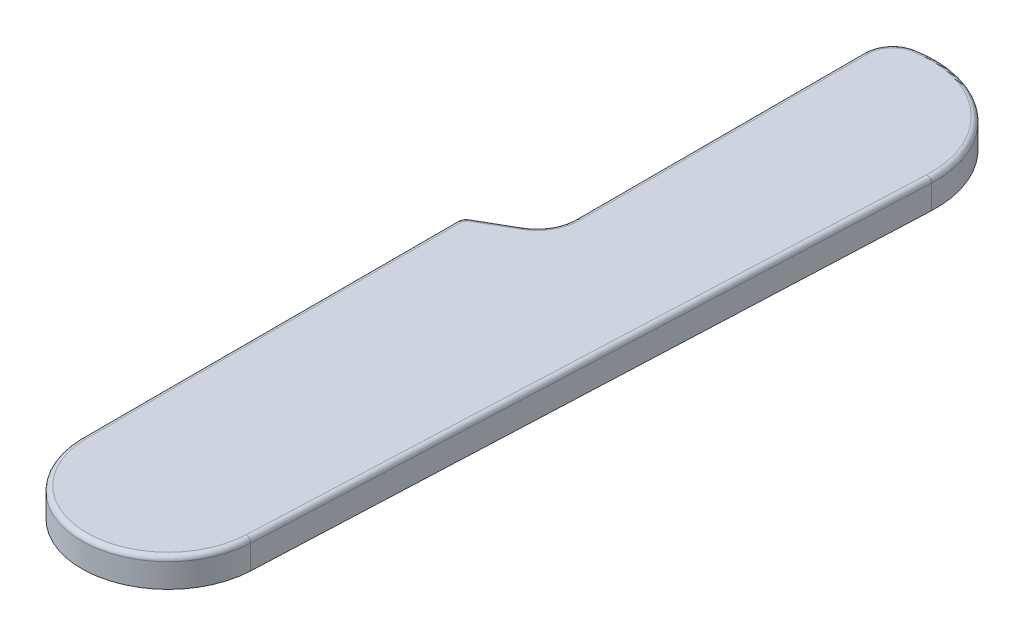
SolidWorks part; units mm, degrees
material "1060 Alloy"
ref_plane "Front Plane" through (0, 0, 0) normal (0, 0, 1) x (1, 0, 0)
ref_plane "Top Plane" through (0, 0, 0) normal (0, 1, 0) x (1, 0, 0)
ref_plane "Right Plane" through (0, 0, 0) normal (1, 0, 0) x (0, 0, -1)
sketch "Sketch1" plane through (0, 0, 0) normal (0, 1, 0) x (1, 0, 0)
  line L0 (0, 9) -> (0, 87.8388) construction
  line L2 (8.9914, -0.3926) -> (11.9574, 67.5386)
  line L3 (-8.9989, -0.1419) -> (-8.9989, 39.6237)
  line L4 (-8.9989, 39.6237) -> (-2.9989, 43.0878)
  line L5 (-2.9989, 43.0878) -> (-2.9989, 77.6237)
  arc A0 (-8.9989, -0.1419) -> (8.9914, -0.3926) centre (0, 0) ccw
  arc A2 (-2.9989, 77.6237) -> (11.9574, 67.5386) centre (1.3902, 68) cw
  dimension "D2" = 18
  dimension "D3" = 68
  dimension "D1" = 120
  dimension "D4" = 6
  dimension "D5" = 38
  dimension "D6" = 2.5
extrude "Boss-Extrude1" add sketch "Sketch1" along normal blind 3 contours A2 L2 A0 L3 L4 L5
fillet "Fillet1" radius 4 1 edges at (-2.9989, 1.5, -43.0878)
fillet "Fillet2" radius 3 1 edges at (-2.9989, 1.5, -77.6237)
fillet "Fillet3" radius 1 1 edges at (-8.9989, 1.5, -39.6237)
fillet "Fillet4" radius 0.5 9 edges at (-8.9989, 3, -19.4522) (-8.8649, 3, -39.5463) (-0.1254, 3, 8.9991) (10.4744, 3, -33.573) (8.3251, 3, -75.9866) (-2.3065, 3, -77.3659) (-2.9989, 3, -60.423) (-3.5348, 3, -43.3972) (-6.7489, 3, -40.9227)
sketch "Sketch2" plane through (0, 0, 0) normal (0, -1, 0) x (-1, 0, 0)
  circle A0 centre (-6.9165, 69.4823) radius 1
  circle A1 centre (-2.7408, 1.6106) radius 1
  circle A2 centre (6, 35.3553) radius 1
extrude "Cut-Extrude1" cut sketch "Sketch2" against normal blind 2.3
